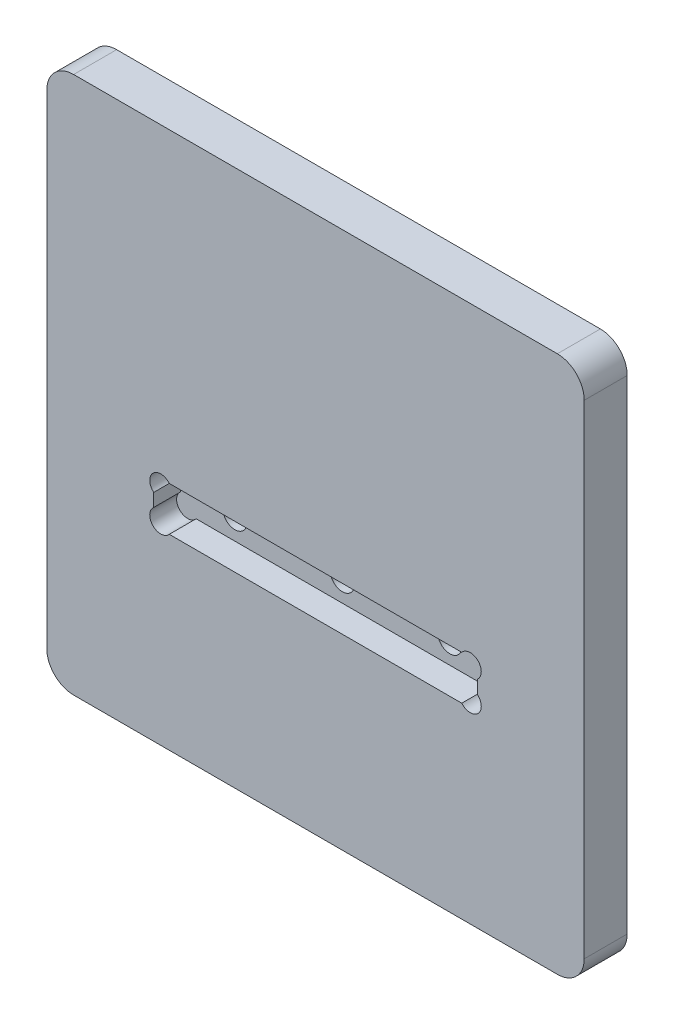
SolidWorks part; units mm, degrees
ref_plane "Front" through (0, 0, 0) normal (0, 0, 1) x (1, 0, 0)
ref_plane "Top" through (0, 0, 0) normal (0, 1, 0) x (1, 0, 0)
ref_plane "Right" through (0, 0, 0) normal (1, 0, 0) x (0, 0, -1)
sketch "Esquisse1" plane through (0, 0, 0) normal (0, 0, 1) x (1, 0, 0)
  line L1 (0, 0) -> (100, 0)
  line L2 (0, 0) -> (0, 100)
  line L3 (0, 100) -> (100, 100)
  line L4 (100, 0) -> (100, 100)
  dimension "D1" = 100
  dimension "D2" = 100
extrude "Boss.-Extru.1" add sketch "Esquisse1" along normal blind 8
sketch "Esquisse2" plane through (0, 0, 8) normal (0, 0, 1) x (1, 0, 0)
  line L1 (19.9, 43) -> (80.1, 43)
  line L2 (19.9, 43) -> (19.9, 34.8)
  line L3 (19.9, 34.8) -> (80.1, 34.8)
  line L4 (80.1, 43) -> (80.1, 34.8)
  line L6 (100, 100) -> (0, 100) construction
  line L7 (50, 34.8) -> (50, 0) construction
  line L8 (0, 0) -> (100, 0) construction
  dimension "D1" = 8.2
  dimension "D2" = 57
  dimension "D3" = 60.2
extrude "Enlèv. mat.-Extru.1" cut sketch "Esquisse2" against normal blind 5
fillet "Congé1" radius 5 4 edges at (100, 0, 4) (0, 0, 4) (0, 100, 4) (100, 100, 4)
sketch "Esquisse3" plane through (0, 0, 8) normal (0, 0, 1) x (1, 0, 0)
  line L0 (80.1, 43) -> (78.7919, 41.6919) construction
  line L1 (80.1, 34.8) -> (80.1, 43) construction
  line L2 (80.1, 43) -> (80.2414, 43.1414) construction
  line L3 (50, 43) -> (50, 34.8) construction
  line L4 (80.1, 43) -> (19.9, 43) construction
  line L5 (19.9, 34.8) -> (80.1, 34.8) construction
  line L6 (80.1, 34.8) -> (80.1, 43) construction
  line L7 (77.2135, 43) -> (80.1, 40.1135)
  line L8 (50, 38.9) -> (55.2954, 38.9) construction
  line L9 (80.1, 34.8) -> (80.2414, 34.6586) construction
  line L10 (80.1, 34.8) -> (78.7919, 36.1081) construction
  line L11 (77.2135, 34.8) -> (80.1, 37.6865)
  line L12 (19.9, 34.8) -> (21.2081, 36.1081) construction
  line L13 (19.9, 34.8) -> (19.7586, 34.6586) construction
  line L14 (19.9, 43) -> (19.7586, 43.1414) construction
  line L15 (19.9, 43) -> (21.2081, 41.6919) construction
  line L16 (22.7865, 34.8) -> (19.9, 37.6865)
  line L17 (22.7865, 43) -> (19.9, 40.1135)
  circle A0 centre (78.7919, 41.6919) radius 2.05 construction
  arc A1 (77.2135, 43) -> (80.1, 40.1135) centre (78.7919, 41.6919) cw
  circle A2 centre (78.7919, 36.1081) radius 2.05 construction
  arc A3 (77.2135, 34.8) -> (80.1, 37.6865) centre (78.7919, 36.1081) ccw
  circle A4 centre (21.2081, 36.1081) radius 2.05 construction
  circle A5 centre (21.2081, 41.6919) radius 2.05 construction
  arc A6 (22.7865, 34.8) -> (19.9, 37.6865) centre (21.2081, 36.1081) cw
  arc A7 (22.7865, 43) -> (19.9, 40.1135) centre (21.2081, 41.6919) ccw
  dimension "D2" = 4.1
  dimension "D1" = 135
  dimension "D3" = 0.2
extrude "Enlèv. mat.-Extru.2" cut sketch "Esquisse3" against normal up to vertex (5 mm away)
sketch "Esquisse4" plane through (0, 0, 3) normal (0, 0, 1) x (1, 0, 0)
  line L0 (19.9, 38.9) -> (80.1, 38.9) construction
  line L1 (19.9, 40.1135) -> (19.9, 37.6865) construction
  line L2 (80.1, 37.6865) -> (80.1, 40.1135) construction
  line L3 (50, 38.9) -> (50, 43) construction
  line L4 (77.2135, 43) -> (22.7865, 43) construction
  circle A0 centre (50, 38.9) radius 2.25
  circle A1 centre (70, 38.9) radius 2.25
  circle A2 centre (30, 38.9) radius 2.25
  dimension "D1" = 20
  dimension "D2" = 4.5
extrude "Enlèv. mat.-Extru.3" cut sketch "Esquisse4" against normal through all both and the other way through all
